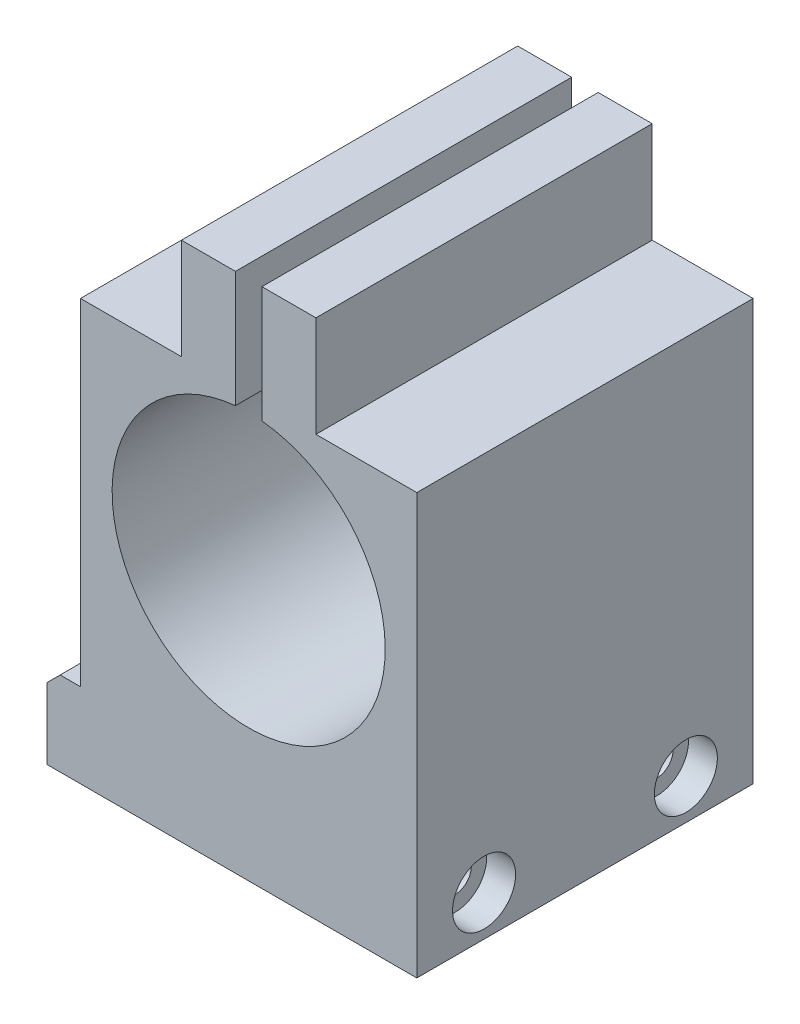
SolidWorks part; units mm, degrees
ref_plane "Front Plane" through (0, 0, 0) normal (0, 0, 1) x (1, 0, 0)
ref_plane "Top Plane" through (0, 0, 0) normal (0, 1, 0) x (1, 0, 0)
ref_plane "Right Plane" through (0, 0, 0) normal (1, 0, 0) x (0, 0, -1)
sketch "Sketch1" plane through (0, 0, 0) normal (0, 0, 1) x (1, 0, 0)
  line L0 (0.1098, 6.35) -> (28.0498, 6.35)
  line L2 (0.1098, 6.35) -> (0.1098, 12.7)
  line L3 (0.1098, 12.7) -> (2.6498, 12.7)
  line L4 (2.6498, 6.35) -> (2.6498, 12.7)
  line L6 (2.6498, 6.35) -> (2.6498, 38.1)
  line L7 (2.6498, 38.1) -> (10.2698, 38.1)
  line L8 (28.0498, 6.35) -> (28.0498, 38.1)
  line L9 (20.4298, 38.1) -> (28.0498, 38.1)
  line L11 (20.4298, 38.1) -> (20.4298, 45.72)
  line L12 (20.4298, 45.72) -> (16.3498, 45.72)
  line L13 (10.2698, 38.1) -> (10.2698, 45.72)
  line L15 (16.3498, 38.1) -> (16.3498, 45.72)
  line L17 (14.3498, 38.1) -> (14.3498, 45.72)
  line L19 (14.3498, 45.72) -> (10.2698, 45.72)
  line L20 (16.3498, 38.1) -> (16.3498, 36.9338)
  line L21 (14.3498, 38.1) -> (14.3498, 36.9338)
  arc A0 (14.3498, 36.9338) -> (16.3498, 36.9338) centre (15.3498, 26.67) ccw
  dimension "D1" = 20.6248
  dimension "D2" = 2.54
  dimension "D3" = 7.62
  dimension "D4" = 25.4
  dimension "D5" = 10.16
  dimension "D6" = 11.43
  dimension "D8" = 2
extrude "Boss-Extrude1" add sketch "Sketch1" along normal blind 25.4
sketch "Sketch2" plane through (28.0498, 0, 0) normal (1, 0, 0) x (0, 0, -1)
  line L0 (-25.4, 6.35) -> (-25.4, 38.1) construction
  line L1 (0, 6.35) -> (0, 38.1) construction
  line L3 (-25.4, 6.35) -> (0, 6.35) construction
  circle A0 centre (-20.32, 9.398) radius 1.27
  circle A1 centre (-5.08, 9.398) radius 1.27
  dimension "D1" = 2.54
  dimension "D2" = 2.54
  dimension "D3" = 5.08
  dimension "D4" = 5.08
  dimension "D5" = 3.048
sketch "Sketch3" plane through (20.4298, 0, 0) normal (1, 0, 0) x (0, 0, -1)
  line L0 (-25.4, 38.1) -> (-25.4, 45.72) construction
  line L2 (0, 38.1) -> (0, 45.72) construction
  point P0 (-19.05, 41.91)
  point P1 (-6.35, 41.91)
  point P4 (-25.4, 41.91)
  dimension "D1" = 6.35
  dimension "D2" = 6.35
chamfer "Chamfer1" distance 1 angle 45 1 edges at (0.1098, 12.7, 12.7)
hole_wizard "CBORE for #2 Socket Head Cap Screw1" positions "Sketch7" profile "Sketch9" counterbore size "#2" standard "ANSI Inch" end condition through all
sketch "Sketch7" plane through (28.0498, 0, 0) normal (1, 0, 0) x (0, 0, -1)
  point P0 (-20.32, 9.398)
  point P3 (-5.08, 9.398)
sketch "Sketch9" plane through (28.0498, 9.398, 20.32) normal (0, 1, 0) x (0, 0, -1)
  line L0 (0, 0) -> (0, 27.94)
  line L1 (0, 27.94) -> (1.2192, 27.94)
  line L3 (1.2192, 27.94) -> (1.2192, 2.1844)
  line L4 (1.2192, 2.1844) -> (2.3812, 2.1844)
  line L5 (2.3812, 2.1844) -> (2.3812, 0)
  line L7 (2.3812, 0) -> (0, 0)
  line L11 (0, -6.35) -> (0, 107.95) construction
  dimension "Thru Hole Dia." = 2.4384
  dimension "Thru Hole Depth" = 27.94
  dimension "C'Bore Dia." = 4.7625
  dimension "C'Bore Depth" = 2.1844
